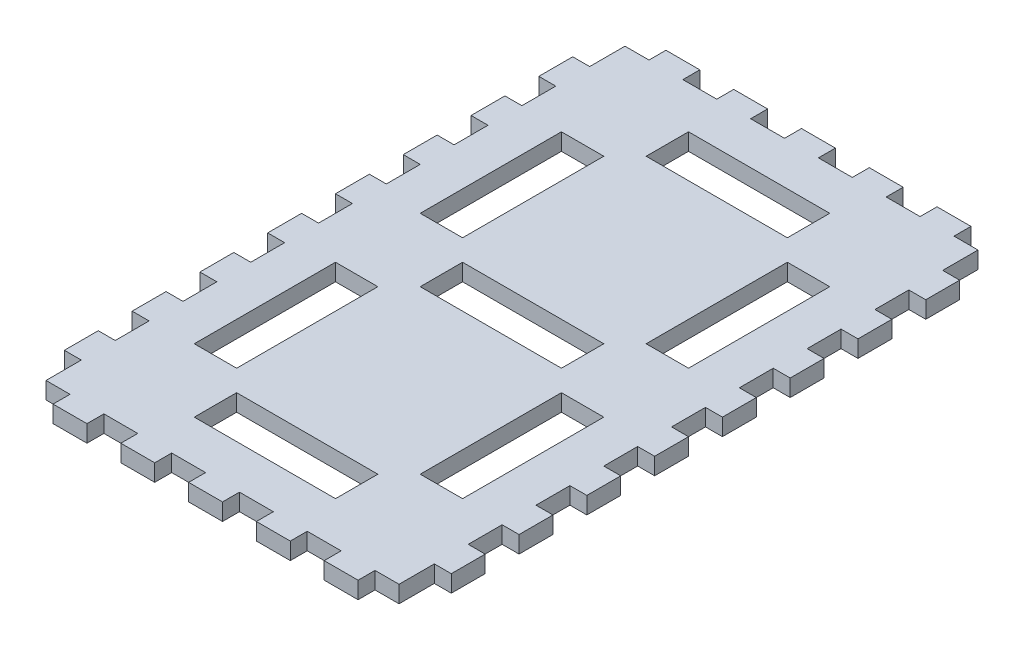
SolidWorks part; units mm, degrees
ref_plane "Front Plane" through (0, 0, 0) normal (0, 0, 1) x (1, 0, 0)
ref_plane "Top Plane" through (0, 0, 0) normal (0, 1, 0) x (1, 0, 0)
ref_plane "Right Plane" through (0, 0, 0) normal (1, 0, 0) x (0, 0, -1)
sketch "Sketch3" plane through (0, 0, 0) normal (0, 1, 0) x (1, 0, 0)
  line L231 (-62.5, -102.5) -> (62.5, -102.5)
  line L232 (-62.5, -102.5) -> (-62.5, 102.5)
  line L233 (-62.5, 102.5) -> (62.5, 102.5)
  line L234 (62.5, -102.5) -> (62.5, 102.5)
  line L235 (-62.5, -102.5) -> (62.5, 102.5) construction
  line L236 (-62.5, 102.5) -> (62.5, -102.5) construction
  point P66 (0, 0)
  dimension "D3" = 205
  dimension "D4" = 125
extrude "Boss-Extrude1" add sketch "Sketch3" along normal blind 6
sketch "Sketch4" plane through (0, 6, 0) normal (0, 1, 0) x (1, 0, 0)
  line L0 (62.5, 102.5) -> (-62.5, 102.5) construction
  line L5 (-32.5, 65) -> (-47.5, 65)
  line L6 (-25, 80) -> (-62.5, 80)
  line L7 (-32.5, 65) -> (-32.5, 15)
  line L8 (-32.5, 15) -> (-47.5, 15)
  line L17 (-25, 87.5) -> (25, 87.5)
  line L18 (-47.5, 65) -> (-47.5, 15)
  line L19 (-25, 87.5) -> (-25, 72.5)
  line L20 (-25, 72.5) -> (25, 72.5)
  line L21 (25, 87.5) -> (25, 72.5)
  line L22 (-62.5, 102.5) -> (-62.5, -102.5) construction
  line L23 (25, 80) -> (62.5, 80)
  line L24 (62.5, -102.5) -> (62.5, 102.5) construction
  line L25 (47.5, 65) -> (47.5, 15)
  line L26 (47.5, 65) -> (32.5, 65)
  line L27 (32.5, 65) -> (32.5, 15)
  line L28 (47.5, 15) -> (32.5, 15)
  line L30 (-25, 7.5) -> (-25, -7.5)
  line L31 (-25, 7.5) -> (25, 7.5)
  line L32 (25, 7.5) -> (25, -7.5)
  line L33 (-25, -7.5) -> (25, -7.5)
  line L34 (-25, -72.5) -> (-25, -87.5)
  line L35 (-25, -72.5) -> (25, -72.5)
  line L36 (25, -72.5) -> (25, -87.5)
  line L37 (-25, -87.5) -> (25, -87.5)
  line L38 (47.5, -15) -> (47.5, -65)
  line L39 (47.5, -15) -> (32.5, -15)
  line L40 (32.5, -15) -> (32.5, -65)
  line L41 (47.5, -65) -> (32.5, -65)
  line L42 (-32.5, -15) -> (-32.5, -65)
  line L43 (-32.5, -15) -> (-47.5, -15)
  line L44 (-47.5, -15) -> (-47.5, -65)
  line L45 (-32.5, -65) -> (-47.5, -65)
  point P16 (0, 87.5)
  dimension "D1" = 15
  dimension "D2" = 37.5
  dimension "D3" = 37.5
  dimension "D4" = 15
  dimension "D6" = 95
  dimension "D7" = 15
  dimension "D8" = 7.5
  dimension "D11" = 15
  dimension "D12" = 7.5
  dimension "D13" = 15
  dimension "D5" = 3
  dimension "D9" = 2
  dimension "D10" = 2
extrude "Cut-Extrude1" cut sketch "Sketch4" against normal blind 6 contours L5 L18 L8 L7 | L28 L25 L26 L27 | L30 L33 L32 L31 | L45 L42 L43 L44 | L41 L38 L39 L40 | L19 L17 L21 L20 | L35 L36 L37 L34
sketch "Sketch5" plane through (0, 6, 0) normal (0, 1, 0) x (1, 0, 0)
  line L0 (62.5, 102.5) -> (-62.5, 102.5) construction
  line L1 (-54, 102.5) -> (-42, 102.5)
  line L2 (-54, 102.5) -> (-54, 108.5)
  line L3 (-54, 108.5) -> (-42, 108.5)
  line L4 (-42, 102.5) -> (-42, 108.5)
  line L5 (-30, 102.5) -> (-30, 108.5)
  line L6 (-30, 102.5) -> (-18, 102.5)
  line L7 (-18, 102.5) -> (-18, 108.5)
  line L8 (-30, 108.5) -> (-18, 108.5)
  line L9 (-6, 102.5) -> (-6, 108.5)
  line L10 (-6, 102.5) -> (6, 102.5)
  line L11 (6, 102.5) -> (6, 108.5)
  line L12 (-6, 108.5) -> (6, 108.5)
  line L13 (18, 102.5) -> (18, 108.5)
  line L14 (18, 102.5) -> (30, 102.5)
  line L15 (30, 102.5) -> (30, 108.5)
  line L16 (18, 108.5) -> (30, 108.5)
  line L17 (42, 102.5) -> (42, 108.5)
  line L18 (42, 102.5) -> (54, 102.5)
  line L19 (54, 102.5) -> (54, 108.5)
  line L20 (42, 108.5) -> (54, 108.5)
  line L41 (-62.5, 102.5) -> (-62.5, -102.5) construction
  line L43 (62.5, -102.5) -> (62.5, 102.5) construction
  line L44 (-62.5, 90) -> (-68.5, 90)
  line L45 (-62.5, 90) -> (-62.5, 78)
  line L46 (-62.5, 78) -> (-68.5, 78)
  line L47 (-68.5, 90) -> (-68.5, 78)
  line L48 (68.5, 90) -> (68.5, 78)
  line L49 (68.5, 90) -> (62.5, 90)
  line L50 (62.5, 90) -> (62.5, 78)
  line L51 (68.5, 78) -> (62.5, 78)
  line L52 (68.5, 66) -> (68.5, 54)
  line L53 (68.5, 66) -> (62.5, 66)
  line L54 (62.5, 66) -> (62.5, 54)
  line L55 (68.5, 54) -> (62.5, 54)
  line L56 (68.5, 42) -> (68.5, 30)
  line L57 (68.5, 42) -> (62.5, 42)
  line L58 (62.5, 42) -> (62.5, 30)
  line L59 (68.5, 30) -> (62.5, 30)
  line L60 (68.5, 18) -> (68.5, 6)
  line L61 (68.5, 18) -> (62.5, 18)
  line L62 (62.5, 18) -> (62.5, 6)
  line L63 (68.5, 6) -> (62.5, 6)
  line L64 (68.5, -6) -> (68.5, -18)
  line L65 (68.5, -6) -> (62.5, -6)
  line L66 (62.5, -6) -> (62.5, -18)
  line L67 (68.5, -18) -> (62.5, -18)
  line L68 (68.5, -30) -> (68.5, -42)
  line L69 (68.5, -30) -> (62.5, -30)
  line L70 (62.5, -30) -> (62.5, -42)
  line L71 (68.5, -42) -> (62.5, -42)
  line L72 (68.5, -54) -> (68.5, -66)
  line L73 (68.5, -54) -> (62.5, -54)
  line L74 (62.5, -54) -> (62.5, -66)
  line L75 (68.5, -66) -> (62.5, -66)
  line L76 (68.5, -78) -> (68.5, -90)
  line L77 (68.5, -78) -> (62.5, -78)
  line L78 (62.5, -78) -> (62.5, -90)
  line L79 (68.5, -90) -> (62.5, -90)
  line L80 (-62.5, 66) -> (-62.5, 54)
  line L81 (-62.5, 66) -> (-68.5, 66)
  line L82 (-68.5, 66) -> (-68.5, 54)
  line L83 (-62.5, 54) -> (-68.5, 54)
  line L84 (-62.5, 42) -> (-62.5, 30)
  line L85 (-62.5, 42) -> (-68.5, 42)
  line L86 (-68.5, 42) -> (-68.5, 30)
  line L87 (-62.5, 30) -> (-68.5, 30)
  line L88 (-62.5, 18) -> (-62.5, 6)
  line L89 (-62.5, 18) -> (-68.5, 18)
  line L90 (-68.5, 18) -> (-68.5, 6)
  line L91 (-62.5, 6) -> (-68.5, 6)
  line L92 (-62.5, -6) -> (-62.5, -18)
  line L93 (-62.5, -6) -> (-68.5, -6)
  line L94 (-68.5, -6) -> (-68.5, -18)
  line L95 (-62.5, -18) -> (-68.5, -18)
  line L96 (-62.5, -30) -> (-62.5, -42)
  line L97 (-62.5, -30) -> (-68.5, -30)
  line L98 (-68.5, -30) -> (-68.5, -42)
  line L99 (-62.5, -42) -> (-68.5, -42)
  line L100 (-62.5, -54) -> (-62.5, -66)
  line L101 (-62.5, -54) -> (-68.5, -54)
  line L102 (-68.5, -54) -> (-68.5, -66)
  line L103 (-62.5, -66) -> (-68.5, -66)
  line L104 (-62.5, -78) -> (-62.5, -90)
  line L105 (-62.5, -78) -> (-68.5, -78)
  line L106 (-68.5, -78) -> (-68.5, -90)
  line L107 (-62.5, -90) -> (-68.5, -90)
  line L108 (-62.5, 6) -> (-62.5, -6)
  line L109 (-54, -108.5) -> (-54, -102.5)
  line L110 (-54, -108.5) -> (-42, -108.5)
  line L111 (-42, -108.5) -> (-42, -102.5)
  line L112 (-54, -102.5) -> (-42, -102.5)
  line L113 (-30, -108.5) -> (-30, -102.5)
  line L114 (-30, -108.5) -> (-18, -108.5)
  line L115 (-18, -108.5) -> (-18, -102.5)
  line L116 (-30, -102.5) -> (-18, -102.5)
  line L117 (-6, -108.5) -> (-6, -102.5)
  line L118 (-6, -108.5) -> (6, -108.5)
  line L119 (6, -108.5) -> (6, -102.5)
  line L120 (-6, -102.5) -> (6, -102.5)
  line L121 (18, -108.5) -> (18, -102.5)
  line L122 (18, -108.5) -> (30, -108.5)
  line L123 (30, -108.5) -> (30, -102.5)
  line L124 (18, -102.5) -> (30, -102.5)
  line L125 (42, -108.5) -> (42, -102.5)
  line L126 (42, -108.5) -> (54, -108.5)
  line L127 (54, -108.5) -> (54, -102.5)
  line L128 (42, -102.5) -> (54, -102.5)
  point P6 (0, 102.5)
  point P7 (0, 0)
  point P8 (-48, 108.5)
  point P55 (-62.5, 0)
  line M6 (62.5, -102.5) -> (62.5, 102.5)
  line M7 (62.5, 102.5) -> (-62.5, 102.5)
  line M8 (-62.5, 102.5) -> (-62.5, -102.5)
  line M9 (-62.5, -102.5) -> (62.5, -102.5)
  dimension "D1" = 12
  dimension "D2" = 6
  dimension "D5" = 12
  dimension "D6" = 205
  dimension "D8" = 12
  dimension "D9" = 6
  dimension "D12" = 125
  dimension "D13" = 24
  dimension "D3" = 5
  dimension "D4" = 2
  dimension "D10" = 2
  dimension "D11" = 8
extrude "Boss-Extrude2" add sketch "Sketch5" against normal blind 6 contours L122 L123 L121 M9 | L118 L119 L117 M9 | L107 L105 L106 M8 | L103 L101 L102 M8 | L95 L93 L94 M8 | L79 L76 L77 M6 | L71 L68 L69 M6 | L67 L64 L65 M6 | L63 L60 L61 M6 | L59 L56 L57 M6 | L51 L48 L49 M6 | L16 L13 L15 M7 | L12 L9 L11 M7 | L8 L5 L7 M7 | L4 L3 L2 M7 | L87 L85 L86 M8 | L91 L89 L90 M8 | L128 L127 L126 L125 | L116 L115 L114 L113 | L112 L111 L110 L109 | L98 L99 L96 L97 | L74 L75 L72 L73 | L52 L55 L54 L53 | L20 L19 L18 L17 | L45 L46 L47 L44 | L82 L83 L80 L81
